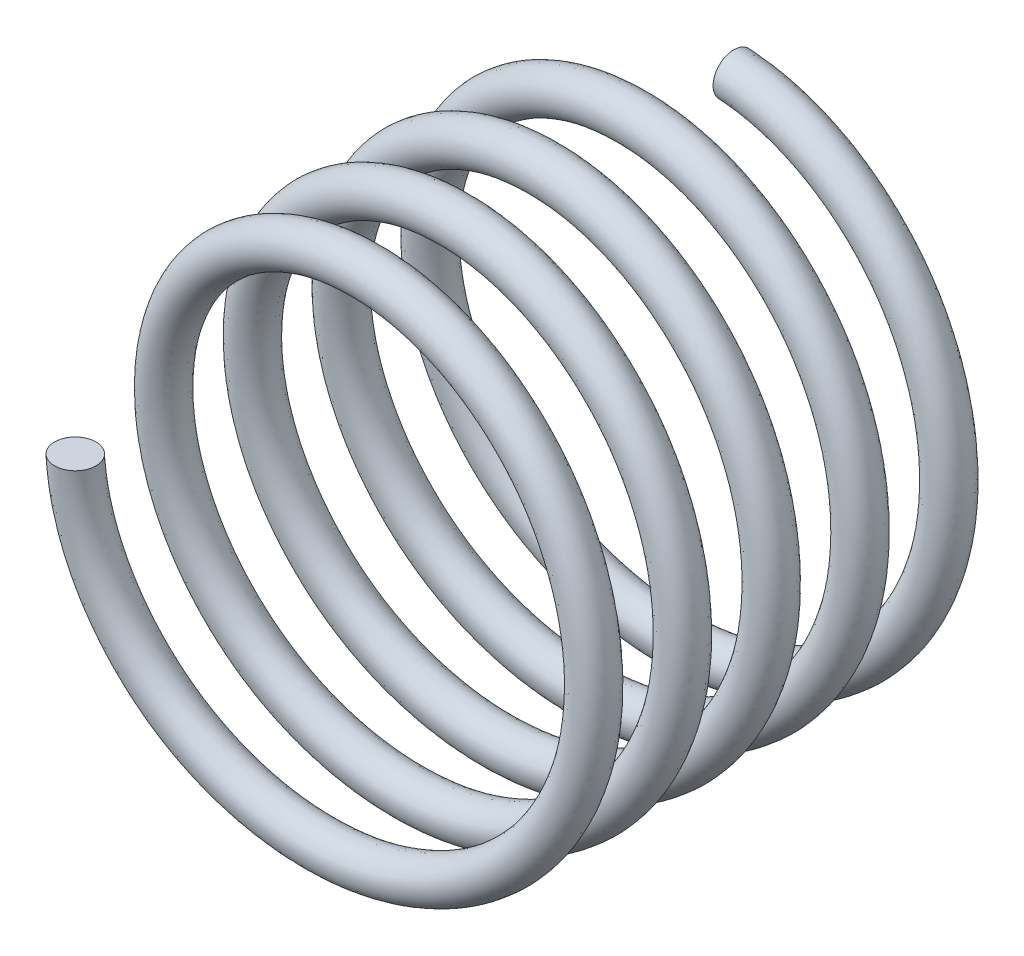
SolidWorks part; units mm, degrees
ref_plane "Front Plane" through (0, 0, 0) normal (0, 0, 1) x (1, 0, 0)
ref_plane "Top Plane" through (0, 0, 0) normal (0, 1, 0) x (1, 0, 0)
ref_plane "Right Plane" through (0, 0, 0) normal (1, 0, 0) x (0, 0, -1)
sketch "Sketch1" plane through (0, 0, 0) normal (0, 0, 1) x (1, 0, 0)
  circle A0 centre (0, 0) radius 2
  dimension "D1" = 4
curve "Helix/Spiral1" pitch 0.75 height 3.5625 turns 4.75
sketch "Sketch3" plane through (0, 0, 0) normal (0, 1, 0) x (1, 0, 0)
  circle A0 centre (-2, -3.5625) radius 0.175
  spline S0 degree 3 poles (999.938, -8.4838) (-43.677, 1.1434) (-6.9909, 0.5008) (1.4508, -0.0937) (1.8959, -0.1406) (2.0521, -0.1875) (1.8959, -0.2344) (1.451, -0.2812) (0.7853, -0.3281) (0, -0.375) (-0.7853, -0.4219) (-1.451, -0.4687) (-1.8959, -0.5156) (-2.0521, -0.5625) (-1.8959, -0.6094) (-1.451, -0.6562) (-0.7853, -0.7031) (0, -0.75) (0.7853, -0.7969) (1.451, -0.8437) (1.8959, -0.8906) (2.0521, -0.9375) (1.8959, -0.9844) (1.451, -1.0313) (0.7853, -1.0781) (0, -1.125) (-0.7853, -1.1719) (-1.451, -1.2188) (-1.8959, -1.2656) (-2.0521, -1.3125) (-1.8959, -1.3594) (-1.451, -1.4063) (-0.7853, -1.4531) (0, -1.5) (0.7853, -1.5469) (1.451, -1.5938) (1.8959, -1.6406) (2.0521, -1.6875) (1.8959, -1.7344) (1.451, -1.7813) (0.7853, -1.8281) (0, -1.875) (-0.7853, -1.9219) (-1.451, -1.9688) (-1.8959, -2.0156) (-2.0521, -2.0625) (-1.8959, -2.1094) (-1.451, -2.1563) (-0.7853, -2.2031) (0, -2.25) (0.7853, -2.2969) (1.451, -2.3438) (1.8959, -2.3906) (2.0521, -2.4375) (1.8959, -2.4844) (1.451, -2.5313) (0.7853, -2.5781) (0, -2.625) (-0.7853, -2.6719) (-1.451, -2.7188) (-1.8959, -2.7656) (-2.0521, -2.8125) (-1.8959, -2.8594) (-1.451, -2.9063) (-0.7853, -2.9531) (0, -3) (0.7853, -3.0469) (1.451, -3.0938) (1.8959, -3.1406) (2.0521, -3.1875) (1.8959, -3.2344) (1.451, -3.2813) (0.7853, -3.3281) (0, -3.375) (-0.7853, -3.4219) (-1.451, -3.4688) (-9.6667, -4.3334) (124.6646, -5.3196) (997.5241, 26.9852) knots -0.46179 -0.46179 -0.46179 -0.46179 0.013158 0.026316 0.039474 0.052632 0.065789 0.078947 0.092105 0.105263 0.118421 0.131579 0.144737 0.157895 0.171053 0.184211 0.197368 0.210526 0.223684 0.236842 0.25 0.263158 0.276316 0.289474 0.302632 0.315789 0.328947 0.342105 0.355263 0.368421 0.381579 0.394737 0.407895 0.421053 0.434211 0.447368 0.460526 0.473684 0.486842 0.5 0.513158 0.526316 0.539474 0.552632 0.565789 0.578947 0.592105 0.605263 0.618421 0.631579 0.644737 0.657895 0.671053 0.684211 0.697368 0.710526 0.723684 0.736842 0.75 0.763158 0.776316 0.789474 0.802632 0.815789 0.828947 0.842105 0.855263 0.868421 0.881579 0.894737 0.907895 0.921053 0.934211 0.947368 0.960526 0.973684 0.986842 1.689573 1.689573 1.689573 1.689573 only from (0, 0) to (-2, -3.5625) construction
  spline S1 degree 3 poles (0, 0) (0.2601, -0.0155) (0.7861, -0.0469) (1.4508, -0.0937) (1.8959, -0.1406) (2.0521, -0.1875) (1.8959, -0.2344) (1.451, -0.2812) (0.7853, -0.3281) (0, -0.375) (-0.7853, -0.4219) (-1.451, -0.4687) (-1.8959, -0.5156) (-2.0521, -0.5625) (-1.8959, -0.6094) (-1.451, -0.6562) (-0.7853, -0.7031) (0, -0.75) (0.7853, -0.7969) (1.451, -0.8437) (1.8959, -0.8906) (2.0521, -0.9375) (1.8959, -0.9844) (1.451, -1.0313) (0.7853, -1.0781) (0, -1.125) (-0.7853, -1.1719) (-1.451, -1.2188) (-1.8959, -1.2656) (-2.0521, -1.3125) (-1.8959, -1.3594) (-1.451, -1.4063) (-0.7853, -1.4531) (0, -1.5) (0.7853, -1.5469) (1.451, -1.5938) (1.8959, -1.6406) (2.0521, -1.6875) (1.8959, -1.7344) (1.451, -1.7813) (0.7853, -1.8281) (0, -1.875) (-0.7853, -1.9219) (-1.451, -1.9688) (-1.8959, -2.0156) (-2.0521, -2.0625) (-1.8959, -2.1094) (-1.451, -2.1563) (-0.7853, -2.2031) (0, -2.25) (0.7853, -2.2969) (1.451, -2.3438) (1.8959, -2.3906) (2.0521, -2.4375) (1.8959, -2.4844) (1.451, -2.5313) (0.7853, -2.5781) (0, -2.625) (-0.7853, -2.6719) (-1.451, -2.7188) (-1.8959, -2.7656) (-2.0521, -2.8125) (-1.8959, -2.8594) (-1.451, -2.9063) (-0.7853, -2.9531) (0, -3) (0.7853, -3.0469) (1.451, -3.0938) (1.8959, -3.1406) (2.0521, -3.1875) (1.8959, -3.2344) (1.451, -3.2813) (0.7853, -3.3281) (0, -3.375) (-0.7853, -3.4219) (-1.451, -3.4688) (-1.8959, -3.5156) (-2, -3.547) (-2, -3.5625) knots 0 0 0 0 0.013158 0.026316 0.039474 0.052632 0.065789 0.078947 0.092105 0.105263 0.118421 0.131579 0.144737 0.157895 0.171053 0.184211 0.197368 0.210526 0.223684 0.236842 0.25 0.263158 0.276316 0.289474 0.302632 0.315789 0.328947 0.342105 0.355263 0.368421 0.381579 0.394737 0.407895 0.421053 0.434211 0.447368 0.460526 0.473684 0.486842 0.5 0.513158 0.526316 0.539474 0.552632 0.565789 0.578947 0.592105 0.605263 0.618421 0.631579 0.644737 0.657895 0.671053 0.684211 0.697368 0.710526 0.723684 0.736842 0.75 0.763158 0.776316 0.789474 0.802632 0.815789 0.828947 0.842105 0.855263 0.868421 0.881579 0.894737 0.907895 0.921053 0.934211 0.947368 0.960526 0.973684 0.986842 1 1 1 1 construction
  dimension "D1" = 0.35
sweep "Sweep1" add profiles "Sketch3" path "Helix/Spiral1"
